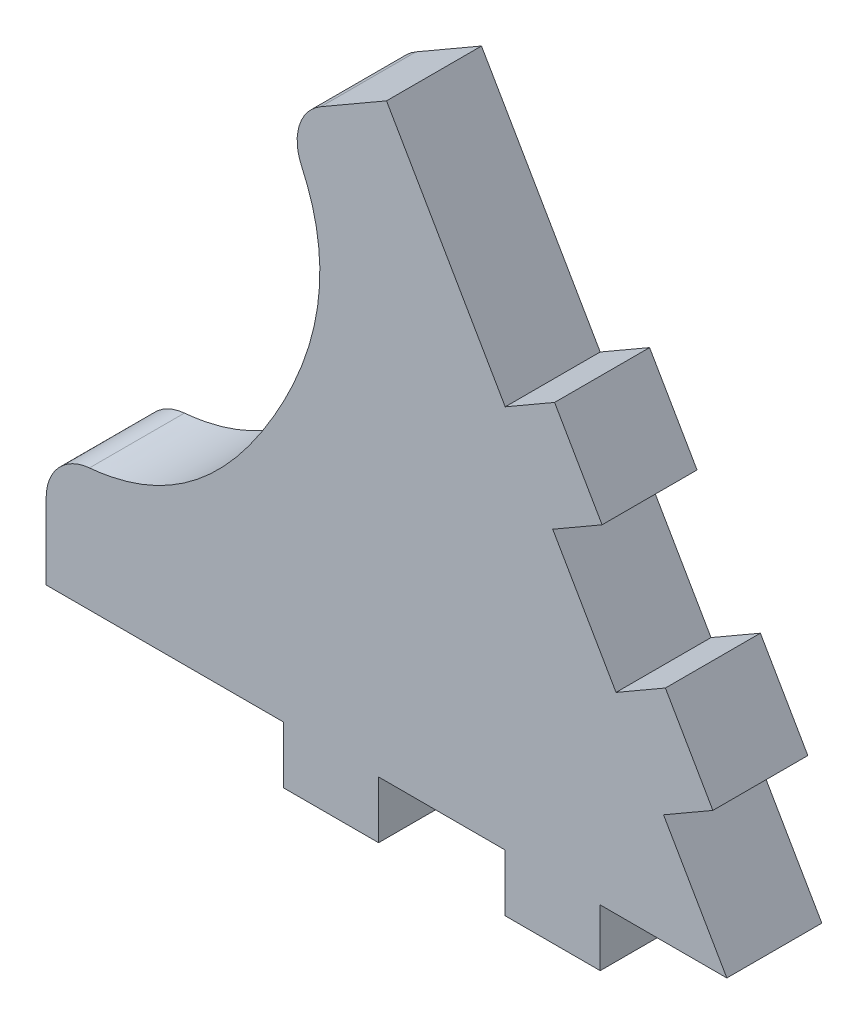
SolidWorks part; units mm, degrees
ref_plane "Front Plane" through (0, 0, 0) normal (0, 0, 1) x (1, 0, 0)
ref_plane "Top Plane" through (0, 0, 0) normal (0, 1, 0) x (1, 0, 0)
ref_plane "Right Plane" through (0, 0, 0) normal (1, 0, 0) x (0, 0, -1)
sketch "Sketch1" plane through (0, 0, 0) normal (0, 0, 1) x (1, 0, 0)
  line L0 (36.6667, -6) -> (36.6667, 0)
  line L1 (46.6667, -6) -> (36.6667, -6)
  line L2 (46.6667, 0) -> (46.6667, -6)
  line L3 (60, 0) -> (46.6667, 0)
  line L4 (-11.6667, 0) -> (-11.6667, 13)
  line L5 (13.3333, 0) -> (-11.6667, 0)
  line L6 (13.3333, -6) -> (13.3333, 0)
  line L7 (23.3333, -6) -> (13.3333, -6)
  line L8 (23.3333, 0) -> (23.3333, -6)
  line L9 (60, 0) -> (53.3333, 11.547)
  line L10 (53.3333, 11.547) -> (58.5295, 14.547)
  line L11 (58.5295, 14.547) -> (53.5295, 23.2073)
  line L12 (53.5295, 23.2073) -> (48.3333, 20.2073)
  line L13 (48.3333, 20.2073) -> (41.6667, 31.7543)
  line L14 (41.6667, 31.7543) -> (46.8628, 34.7543)
  line L15 (46.8628, 34.7543) -> (41.8628, 43.4145)
  line L16 (41.8628, 43.4145) -> (36.6667, 40.4145)
  line L17 (36.6667, 40.4145) -> (24.1667, 62.0652)
  line L18 (24.1667, 62.0652) -> (12.9083, 55.5652)
  line L19 (36.6667, 0) -> (23.3333, 0)
  line L20 (60, 0) -> (-26.6025, 50) construction
  line L21 (60, 0) -> (12.3686, 27.5) construction
  spline S0 degree 3 poles (12.9083, 55.5652) (18.7925, 47.4128) (18.5015, 38.1225) (12.3686, 27.5) knots 0 0 0 0 1 1 1 1
  spline S1 degree 3 poles (-11.6667, 13) (-1.6645, 11.9804) (6.2357, 16.8775) (12.3686, 27.5) knots 0 0 0 0 1 1 1 1
  dimension "D1" = 13
  dimension "D2" = 10
  dimension "D3" = 25
  dimension "D4" = 6
  dimension "D5" = 30
  dimension "D6" = 100
  dimension "D7" = 55
  dimension "D8" = 13.3333
extrude "Boss-Extrude1" add sketch "Sketch1" along normal blind 10
fillet "Fillet1" radius 5 2 edges at (-11.6667, 13, 5) (12.9083, 55.5652, 5)
